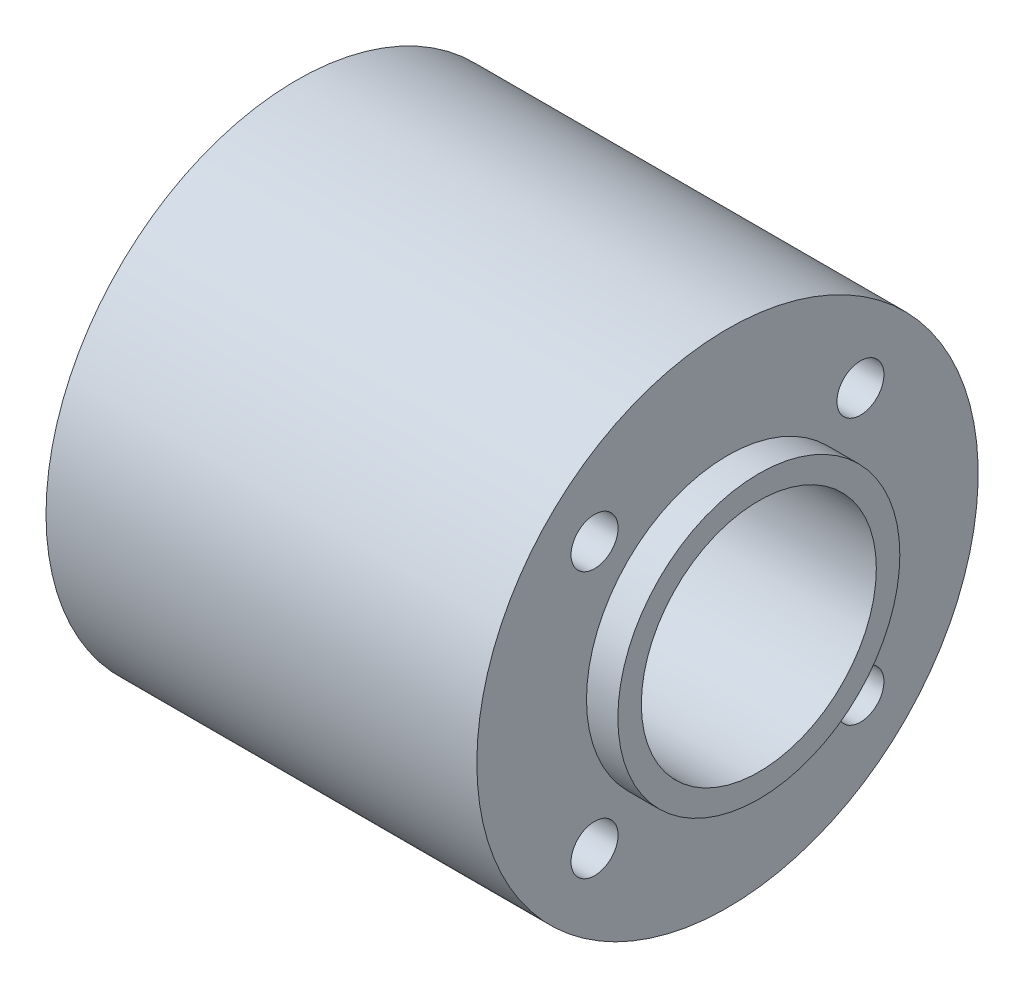
SolidWorks part; units mm, degrees
ref_plane "Front Plane" through (0, 0, 0) normal (0, 0, 1) x (1, 0, 0)
ref_plane "Top Plane" through (0, 0, 0) normal (0, 1, 0) x (1, 0, 0)
ref_plane "Right Plane" through (0, 0, 0) normal (1, 0, 0) x (0, 0, -1)
sketch "Sketch1" plane through (0, 0, 0) normal (0, 0, 1) x (1, 0, 0)
  line L0 (0, 0) -> (45.8668, 0) construction
  line L1 (0, 7.5) -> (0, 9)
  line L2 (0, 9) -> (2, 9)
  line L3 (2, 9) -> (2, 16)
  line L4 (2, 16) -> (29.5, 16)
  line L5 (29.5, 16) -> (29.5, 9)
  line L6 (29.5, 9) -> (31.5, 9)
  line L7 (31.5, 9) -> (31.5, 7.5)
  line L8 (0, 7.5) -> (31.5, 7.5)
  point P11 (29.5, 12.5)
  dimension "D1" = 2
  dimension "D2" = 27.5
  dimension "D3" = 2
  dimension "D4" = 7.5
  dimension "D5" = 9
  dimension "D6" = 16
revolve "Revolve1" add sketch "Sketch1" angle 360 about L0
sketch "Sketch2" plane through (2, 0, 0) normal (-1, 0, 0) x (0, 0, 1)
  line L0 (0, 0) -> (0, 16) construction
  line L1 (0, 0) -> (8.4853, 8.4853) construction
  circle A0 centre (0, 0) radius 12 construction
  circle A1 centre (0, 0) radius 16 construction
  circle A2 centre (8.4853, 8.4853) radius 1.5
  dimension "D1" = 24
  dimension "D3" = 3
  dimension "D2" = 45
extrude "Cut-Extrude1" cut sketch "Sketch2" against normal through all
pattern_circular "CirPattern1" count 4 over 360 about axis through (0, 0, 0) along (1, 0, 0) of "Cut-Extrude1"
scale "Scale1" scale about centroid uniform scaling yes scale factor 1.7
